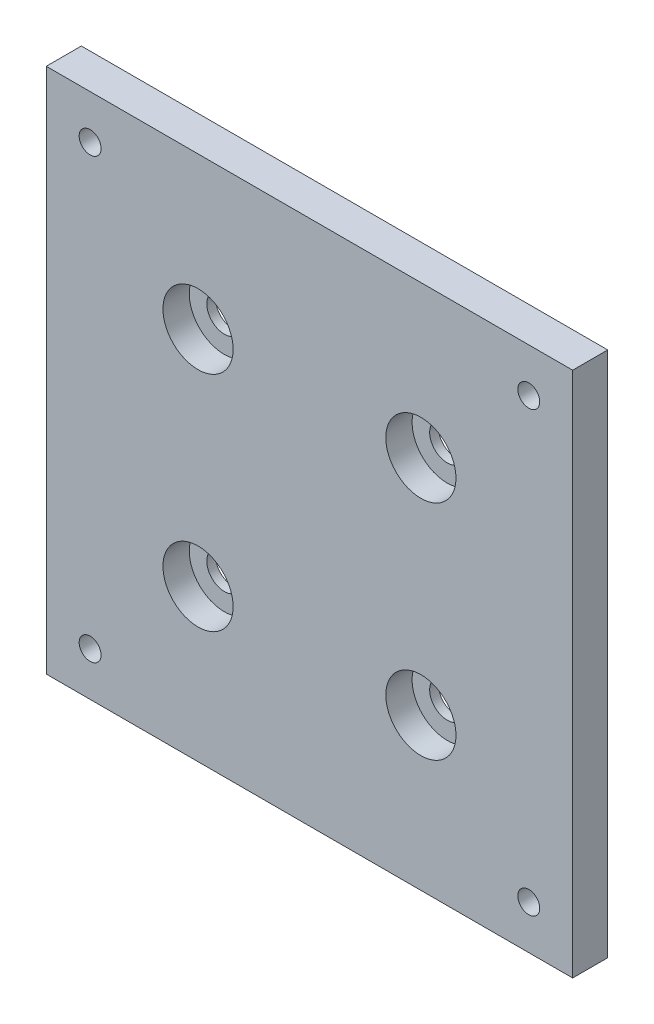
SolidWorks part; units mm, degrees
ref_plane "前视基准面" through (0, 0, 0) normal (0, 0, 1) x (1, 0, 0)
ref_plane "上视基准面" through (0, 0, 0) normal (0, 1, 0) x (1, 0, 0)
ref_plane "右视基准面" through (0, 0, 0) normal (1, 0, 0) x (0, 0, -1)
sketch "草图1" plane through (0, 0, 0) normal (0, 0, 1) x (1, 0, 0)
  line L1 (-30, 30) -> (30, 30)
  line L2 (-30, 30) -> (-30, -30)
  line L3 (-30, -30) -> (30, -30)
  line L4 (30, 30) -> (30, -30)
  line L5 (-30, 30) -> (30, -30) construction
  line L6 (-30, -30) -> (30, 30) construction
  point P0 (0, 0)
  dimension "D1" = 60
extrude "凸台-拉伸1" add sketch "草图1" along normal blind 4
sketch "草图2" plane through (0, 0, 4) normal (0, 0, 1) x (1, 0, 0)
  line L1 (25, -25) -> (-25, -25) construction
  line L2 (25, -25) -> (25, 25) construction
  line L3 (25, 25) -> (-25, 25) construction
  line L4 (-25, -25) -> (-25, 25) construction
  line L5 (25, -25) -> (-25, 25) construction
  line L6 (25, 25) -> (-25, -25) construction
  line L7 (12.7, -12.7) -> (-12.7, -12.7) construction
  line L8 (12.7, -12.7) -> (12.7, 12.7) construction
  line L9 (12.7, 12.7) -> (-12.7, 12.7) construction
  line L10 (-12.7, -12.7) -> (-12.7, 12.7) construction
  line L11 (12.7, -12.7) -> (-12.7, 12.7) construction
  line L12 (12.7, 12.7) -> (-12.7, -12.7) construction
  point P0 (0, 0)
  point P6 (0, 0)
  dimension "D1" = 25.4
  dimension "D2" = 50
hole_wizard "M3 螺纹孔1" positions "3D草图1" profile "草图3" tap size "M3" standard "ISO" end condition through all
sketch3d "3D草图1"
  point P0 (-25, 25, 4)
  point P3 (25, 25, 4)
  point P6 (25, -25, 4)
  point P9 (-25, -25, 4)
sketch "草图3" plane through (-25, 25, 4) normal (1, 0, 0) x (0, -1, 0)
  line L0 (0, 0) -> (0, 4)
  line L1 (0, 4) -> (1.25, 4)
  line L2 (1.25, 4) -> (1.25, 0)
  line L5 (1.25, 0) -> (0, 0)
  line L11 (0, -6.35) -> (0, 107.95) construction
  dimension "通孔螺纹孔钻头直径" = 2.5
  dimension "通孔螺纹孔钻头深度" = 4
cosmetic thread "孔螺蚊线1" parameters "D2"=3
cosmetic thread "孔螺蚊线2" parameters "D2"=3
cosmetic thread "孔螺蚊线3" parameters "D2"=3
cosmetic thread "孔螺蚊线4" parameters "D2"=3
hole_wizard "孔1" positions "3D草图2" profile "草图4" legacy end condition through all
sketch3d "3D草图2"
  point P0 (-12.7, 12.7, 4)
  point P3 (12.7, 12.7, 4)
  point P6 (12.7, -12.7, 4)
  point P9 (-12.7, -12.7, 4)
sketch "草图4" plane through (-12.7, 12.7, 4) normal (1, 0, 0) x (0, -1, 0)
  line L0 (0, 0) -> (0, 4)
  line L1 (0, 4) -> (2, 4)
  line L2 (2, 4) -> (2, 3)
  line L3 (2, 3) -> (4, 3)
  line L4 (4, 3) -> (4, 0)
  line L5 (4, 0) -> (0, 0)
  line L6 (0, 110) -> (0, -10) construction
  dimension "直径" = 4
  dimension "深度" = 4
  dimension "柱坑直径" = 8
  dimension "柱坑深度" = 3
